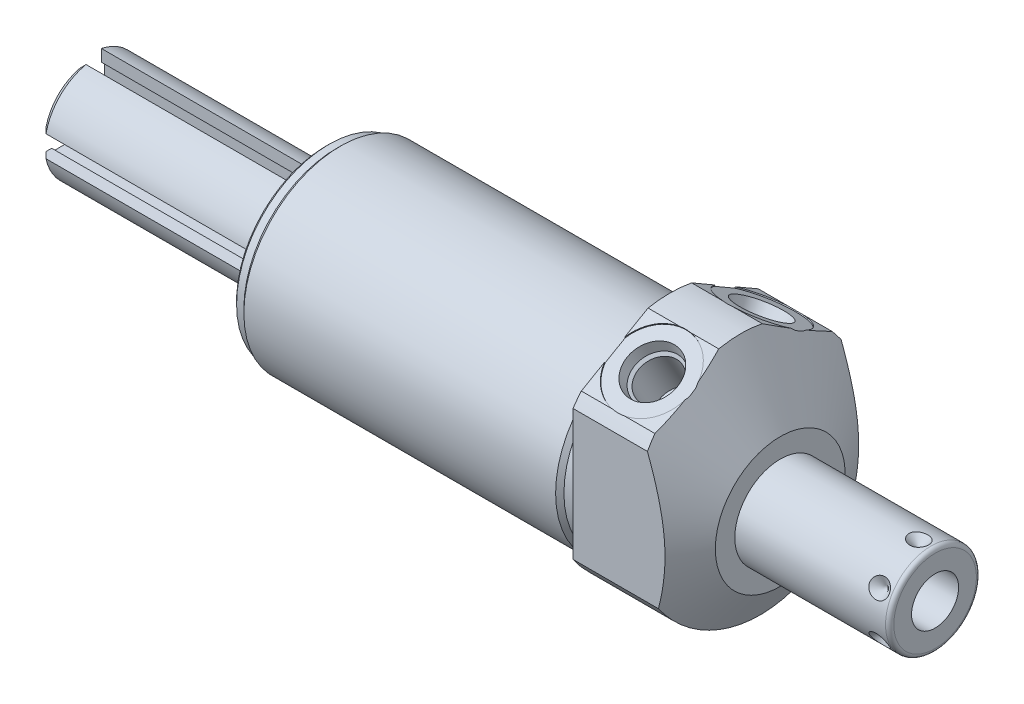
SolidWorks part; units mm, degrees
material "Alloy Steel"
ref_plane "Front Plane" through (0, 0, 0) normal (0, 0, 1) x (1, 0, 0)
ref_plane "Top Plane" through (0, 0, 0) normal (0, 1, 0) x (1, 0, 0)
ref_plane "Right Plane" through (0, 0, 0) normal (1, 0, 0) x (0, 0, -1)
ref_plane "Plane1" through (0, 0, 0) normal (1, 0, 0) x (0, 0, -1)
sketch "Sketch1" plane through (0, 0, 0) normal (1, 0, 0) x (0, 0, -1)
  circle A0 centre (0, 0) radius 28.575
  dimension "D1" = 57.15
extrude "Extrude1" add sketch "Sketch1" along normal blind 27.0002 and the other way blind 84.1248
ref_plane "Plane2" through (0, 0, 0) normal (1, 0, 0) x (0, 0, -1)
sketch "Sketch2" plane through (0, 0, 0) normal (1, 0, 0) x (0, 0, -1)
  line L0 (-25.9842, -4.191) -> (25.9842, -4.191) construction
  circle A0 centre (0, -4.191) radius 23.622
  circle A2 centre (0, 0) radius 28.575
  circle A3 centre (0, 0) radius 28.575
  dimension "D2" = 47.244
  dimension "D1" = 4.191
  dimension "D3" = 0
extrude "Cut-Extrude1" cut sketch "Sketch2" against normal up to next
ref_plane "Plane4" through (0, 0, 0) normal (-1, 0, 0) x (0, 0, 1)
sketch "Sketch4" plane through (0, 0, 0) normal (-1, 0, 0) x (0, 0, 1)
  line L0 (23.6855, -25.6662) -> (23.6855, 17.4761)
  line L1 (23.6855, 17.4761) -> (0, 31.1509)
  line L2 (-23.6855, -25.6662) -> (-23.6855, 17.4761)
  line L3 (-23.6855, 17.4761) -> (0, 31.1509)
  line L4 (0, -31.5613) -> (0, 34.1372) construction
  arc A2 (23.6855, -25.6662) -> (-23.6855, -25.6662) centre (0, 0) ccw
  dimension "D4" = 69.85
  dimension "D1" = 47.371
  dimension "D2" = 30.607
  dimension "D3" = 120
extrude "Cut-Extrude3" cut sketch "Sketch4" against normal up to next
ref_plane "Plane6" through (0, 0, 0) normal (0, 0, 1) x (1, 0, 0)
sketch "Sketch6" plane through (0, 0, 0) normal (0, 0, 1) x (1, 0, 0)
  line L0 (0.7504, 57.15) -> (27.0002, 11.684)
  line L1 (-0.5621, -4.191) -> (28.3127, -4.191) construction
  line L2 (-84.1248, -4.191) -> (0, -4.191) construction
  line L3 (27.0002, 11.684) -> (27.0002, 57.15)
  line L4 (27.0002, 57.15) -> (0.7504, 57.15)
  line L5 (27.0002, 15.9852) -> (27.0002, -15.9852) construction
  dimension "D1" = 60
  dimension "D2" = 31.75
  dimension "D3" = 122.682
revolve "Cut-Revolve2" cut sketch "Sketch6" angle 360 about L1
ref_plane "Plane7" through (9.0932, 23.1369, 13.3727) normal (1, 0, 0) x (0, 0.5, -0.866)
sketch "S2D0002" plane through (9.0932, 23.1369, 13.3727) normal (1, 0, 0) x (0, 0.5, -0.866)
  line L0 (0, 0) -> (6.1849, 0)
  line L1 (6.1849, 0) -> (5.6423, -2.5527)
  line L2 (5.6423, -2.5527) -> (4.9784, -3.2166)
  line L3 (4.9784, -3.2166) -> (4.9784, -13.462)
  line L4 (4.9784, -13.462) -> (0, -13.462)
  line L5 (0, -13.462) -> (0, 0)
  line L6 (0, -14.1351) -> (0, 0.6731) construction
  dimension "D1" = 13.462
revolve "Cut-Revolve3" cut sketch "S2D0002" angle 360 about L6
ref_plane "Plane8" through (9.0932, 23.1369, -13.3727) normal (1, 0, 0) x (0, -0.5, -0.866)
sketch "Sketch8" plane through (9.0932, 23.1369, -13.3727) normal (1, 0, 0) x (0, -0.5, -0.866)
  line L0 (0, 0) -> (6.1849, 0)
  line L1 (6.1849, 0) -> (5.6423, -2.5527)
  line L2 (5.6423, -2.5527) -> (4.9784, -3.2166)
  line L3 (4.9784, -3.2166) -> (4.9784, -13.462)
  line L4 (4.9784, -13.462) -> (0, -13.462)
  line L5 (0, -13.462) -> (0, 0)
  line L6 (0, -14.1351) -> (0, 0.6731) construction
  dimension "D1" = 13.462
revolve "Cut-Revolve4" cut sketch "Sketch8" angle 360 about L6
ref_plane "Plane10" through (0, 0, 0) normal (0, 0, 1) x (1, 0, 0)
sketch "Sketch18" plane through (0, 23.3632, 13.4887) normal (0, 0.866, 0.5) x (1, 0, 0)
  circle A0 centre (9.0932, -0.0127) radius 9.525
  dimension "D1" = 19.05
extrude "Cut-Extrude4" cut sketch "Sketch18" against normal blind 0.254
sketch "Sketch19" plane through (0, 23.3632, -13.4887) normal (0, 0.866, -0.5) x (1, 0, 0)
  circle A0 centre (9.0932, 0.0127) radius 9.525
  circle A1 centre (9.0932, 0.0127) radius 6.1849 construction
  dimension "D1" = 19.05
extrude "Cut-Extrude5" cut sketch "Sketch19" against normal blind 0.254
sketch "Sketch10" plane through (0, 0, 0) normal (0, 0, 1) x (1, 0, 0)
  line L0 (0, 19.431) -> (0, 18.415)
  line L1 (0, 18.415) -> (-3.302, 18.415)
  line L2 (-3.302, 18.415) -> (-4.318, 19.431)
  line L3 (-4.5339, -4.191) -> (0.2159, -4.191) construction
  line L4 (0, 19.431) -> (-4.318, 19.431)
  line L5 (-84.1248, -4.191) -> (0, -4.191) construction
  line L6 (0, 19.431) -> (-84.1248, 19.431) construction
  line L7 (0, 21.9392) -> (0, 18.6529) construction
  dimension "D1" = 45.212
  dimension "D2" = 45
  dimension "D3" = 3.302
revolve "Cut-Revolve6" cut sketch "Sketch10" angle 360 about L3
ref_plane "Plane12" through (0, 0, 0) normal (0, 0, 1) x (1, 0, 0)
sketch "Sketch12" plane through (0, 0, 0) normal (0, 0, 1) x (1, 0, 0)
  line L0 (-84.1248, 19.431) -> (-84.1248, 18.415)
  line L1 (-84.1248, 18.415) -> (-81.5848, 18.415)
  line L2 (-81.5848, 18.415) -> (-80.5688, 19.431)
  line L3 (-84.3026, -4.191) -> (-80.391, -4.191) construction
  line L4 (-84.1248, 19.431) -> (-80.5688, 19.431)
  line L5 (-84.1248, -4.191) -> (-4.318, -4.191) construction
  line L6 (-4.318, 19.431) -> (-84.1248, 19.431) construction
  line L7 (-84.1248, 19.431) -> (-84.1248, -27.813) construction
  dimension "D1" = 45.212
  dimension "D2" = 45
  dimension "D3" = 2.54
revolve "Cut-Revolve8" cut sketch "Sketch12" angle 360 about L3
chamfer "Chamfer1" distance 0.762 angle 45 1 edges at (-84.1248, -4.191, 22.606)
ref_plane "Plane13" through (0, 0, 0) normal (0, 0, 1) x (0, -1, 0)
sketch "Sketch13" plane through (0, 0, 0) normal (0, 0, 1) x (0, -1, 0)
  line L0 (4.191, 27.0002) -> (4.191, 64.8716)
  line L1 (4.191, 64.8716) -> (14.2875, 64.8716)
  line L2 (15.3035, 63.8556) -> (15.3035, 27.0002)
  line L3 (15.3035, 27.0002) -> (4.191, 27.0002)
  line L4 (4.191, 25.1066) -> (4.191, 66.7652) construction
  line L5 (4.191, -80.5688) -> (4.191, -4.318) construction
  line L6 (20.066, 27.0002) -> (-11.684, 27.0002) construction
  line L7 (-18.415, 0) -> (26.797, 0) construction
  arc A0 (15.3035, 63.8556) -> (14.2875, 64.8716) centre (14.2875, 63.8556) ccw
  dimension "D3" = 1.016
  dimension "D1" = 22.225
  dimension "D2" = 64.8716
revolve "Revolve1" add sketch "Sketch13" angle 360 about L4
ref_plane "Plane14" through (64.8716, -9.9441, 0) normal (0, 0, 1) x (0, -1, 0)
sketch "S2D0001" plane through (64.8716, -9.9441, 0) normal (0, 0, 1) x (0, -1, 0)
  line L0 (0, 0) -> (0, -17.018)
  line L1 (0, -17.018) -> (-5.7531, -20.4748)
  line L2 (0, 0) -> (-5.7531, 0)
  line L3 (-5.7531, 0) -> (-5.7531, -20.4748)
  line L4 (-5.7531, -21.4986) -> (-5.7531, 1.0237) construction
  line L5 (-5.7531, -1.016) -> (-5.7531, -37.8714) construction
  line L6 (4.3434, 0) -> (-15.8496, 0) construction
  dimension "D1" = 11.5062
  dimension "D2" = 59
  dimension "D3" = 17.018
revolve "Cut-Revolve9" cut sketch "S2D0001" angle 360 about L4
ref_plane "Plane16" through (60.9092, -15.3035, 0) normal (0, 0, 1) x (-1, 0, 0)
ref_plane "Plane17" through (0, -3.1433, -1.8148) normal (0, 0.866, 0.5) x (-1, 0, 0)
sketch "Sketch16" plane through (60.9092, 6.9215, 0) normal (0, 0, -1) x (-1, 0, 0)
  line L0 (0, 0) -> (2.413, 0)
  line L1 (2.413, 0) -> (0, -2.413)
  line L2 (0, 0) -> (0, -2.413)
  line L3 (0, -4.4865) -> (0, 0.1207) construction
  line L4 (-3.9624, -1.016) -> (-3.9624, -21.209) construction
  line L5 (33.909, 0) -> (-2.9464, 0) construction
  dimension "D1" = 45
  dimension "D2" = 3.9624
  dimension "D3" = 4.826
revolve "Cut-Revolve10" cut sketch "Sketch16" angle 360 about L3
pattern_circular "CirPattern1" count 6 over 360 about axis through (25.1066, -4.191, 0) along (-1, 0, 0) of "Cut-Revolve10"
sketch "Sketch20" plane through (-84.1248, 0, 0) normal (-1, 0, 0) x (0, 0, 1)
  circle A0 centre (0, -4.191) radius 21.0312
  circle A1 centre (0, -4.191) radius 21.844 construction
  dimension "D1" = 42.0624
extrude "Cut-Extrude9" cut sketch "Sketch20" against normal blind 0.127
sketch "Sketch22" plane through (-84.1248, 0, 0) normal (-1, 0, 0) x (0, 0, 1)
  circle A0 centre (0, -4.191) radius 20.7772
  circle A1 centre (0, -4.191) radius 21.0312
  circle A4 centre (0, -4.191) radius 22.606 construction
  circle A5 centre (0, -4.191) radius 21.0312 construction
  dimension "D1" = 41.5544
extrude "Cut-Extrude10" cut sketch "Sketch22" against normal blind 1.524
sketch "Sketch23" plane through (-83.9978, 0, 0) normal (-1, 0, 0) x (0, 0, 1)
  circle A0 centre (0, -4.191) radius 12.7
  circle A1 centre (0, -4.191) radius 20.7772 construction
  dimension "D1" = 25.4
extrude "Extrude2" add sketch "Sketch23" along normal blind 57.6834
sketch "Sketch24" plane through (-141.6812, 0, 0) normal (-1, 0, 0) x (0, 0, 1)
  line L0 (-27.3266, -4.191) -> (29.2926, -4.191) construction
  line L1 (12.4222, -1.5494) -> (9.5123, -1.5494)
  line L2 (9.5123, -1.5494) -> (9.5123, -0.762)
  line L3 (9.5123, -0.762) -> (6.2103, -0.762)
  line L4 (6.2103, -0.762) -> (6.2103, -7.62)
  line L5 (12.4222, -6.8326) -> (9.5123, -6.8326)
  line L6 (9.5123, -6.8326) -> (9.5123, -7.62)
  line L7 (9.5123, -7.62) -> (6.2103, -7.62)
  circle A1 centre (0, -4.191) radius 12.7
  arc A2 (12.4222, -6.8326) -> (12.4222, -1.5494) centre (0, -4.191) ccw
  dimension "D2" = 5.2832
  dimension "D3" = 6.858
  dimension "D4" = 3.302
  dimension "D5" = 6.4897
  dimension "D1" = 0
extrude "Cut-Extrude11" cut sketch "Sketch24" against normal offset from surface (52.9082 mm away) 6.1722 up to face at (-82.6008, -4.191, 20.7772)
sketch "Sketch25" plane through (0, 0, 6.2103) normal (0, 0, 1) x (1, 0, 0)
  line L0 (-141.6812, -4.191) -> (-88.773, -4.191) construction
  line L1 (-88.773, -1.5494) -> (-88.773, -6.8326) construction
  circle A0 centre (-88.773, -4.191) radius 3.429
  dimension "D1" = 6.858
extrude "Cut-Extrude12" cut sketch "Sketch25" along normal through all
pattern_circular "CirPattern2" count 4 over 360 about axis through (0, -4.191, 0) along (1, 0, 0) of "Cut-Extrude11", "Cut-Extrude12"
chamfer "Chamfer2" distance 1.524 angle 45 2 edges at (-141.6812, 4.7893, 8.9803) (-141.6812, -13.1713, 8.9803)
